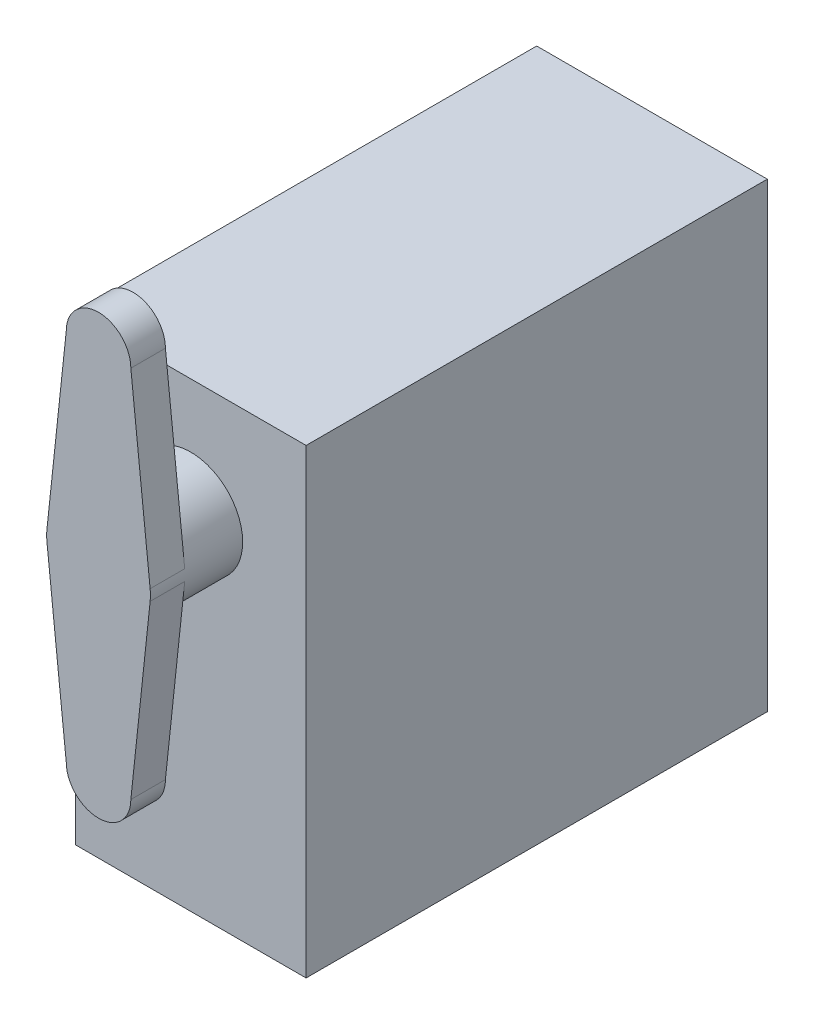
SolidWorks part; units mm, degrees
ref_plane "Front Plane" through (0, 0, 0) normal (0, 0, 1) x (1, 0, 0)
ref_plane "Top Plane" through (0, 0, 0) normal (0, 1, 0) x (1, 0, 0)
ref_plane "Right Plane" through (0, 0, 0) normal (1, 0, 0) x (0, 0, -1)
sketch "Sketch2" plane through (0, 0, 0) normal (0, 0, 1) x (1, 0, 0)
  line L1 (-10, 20) -> (10, 20)
  line L2 (-10, 20) -> (-10, -20)
  line L3 (-10, -20) -> (10, -20)
  line L4 (10, 20) -> (10, -20)
  line L5 (-10, 20) -> (10, -20) construction
  line L6 (-10, -20) -> (10, 20) construction
  point P0 (0, 0)
  dimension "D1" = 20
  dimension "D2" = 40
extrude "Boss-Extrude1" add sketch "Sketch2" along normal blind 40
sketch "Sketch3" plane through (0, 0, 40) normal (0, 0, 1) x (1, 0, 0)
  line L0 (0, 20) -> (0, 10)
  line L1 (-10, 20) -> (10, 20)
  line L2 (-10, 20) -> (-10, -20)
  line L3 (-10, -20) -> (10, -20)
  line L4 (10, 20) -> (10, -20)
  circle A0 centre (0, 10) radius 4.5
extrude "Boss-Extrude2" add sketch "Sketch3" along normal blind 5
ref_plane "Plane4" through (0, 0, 45) normal (0, 0, 1) x (1, 0, 0)
sketch "Sketch5" plane through (0, 0, 45) normal (0, 0, 1) x (1, 0, 0)
  line L0 (4.4747, 9.5234) -> (2.8, -6.2)
  line L2 (-4.4747, 10.4766) -> (-2.8, 26.2)
  line L3 (4.4747, 10.4766) -> (2.8, 26.2)
  line L4 (-4.4747, 9.5234) -> (-2.8, -6.2)
  arc A0 (-4.4747, 10.4766) -> (-4.4747, 9.5234) centre (0, 10) ccw
  arc A1 (2.8, 26.2) -> (-2.8, 26.2) centre (0, 26.2) ccw
  arc A2 (2.8, -6.2) -> (-2.8, -6.2) centre (0, -6.2) cw
  arc A3 (4.4747, 9.5234) -> (4.4747, 10.4766) centre (0, 10) ccw
extrude "Boss-Extrude3" add sketch "Sketch5" along normal blind 3
